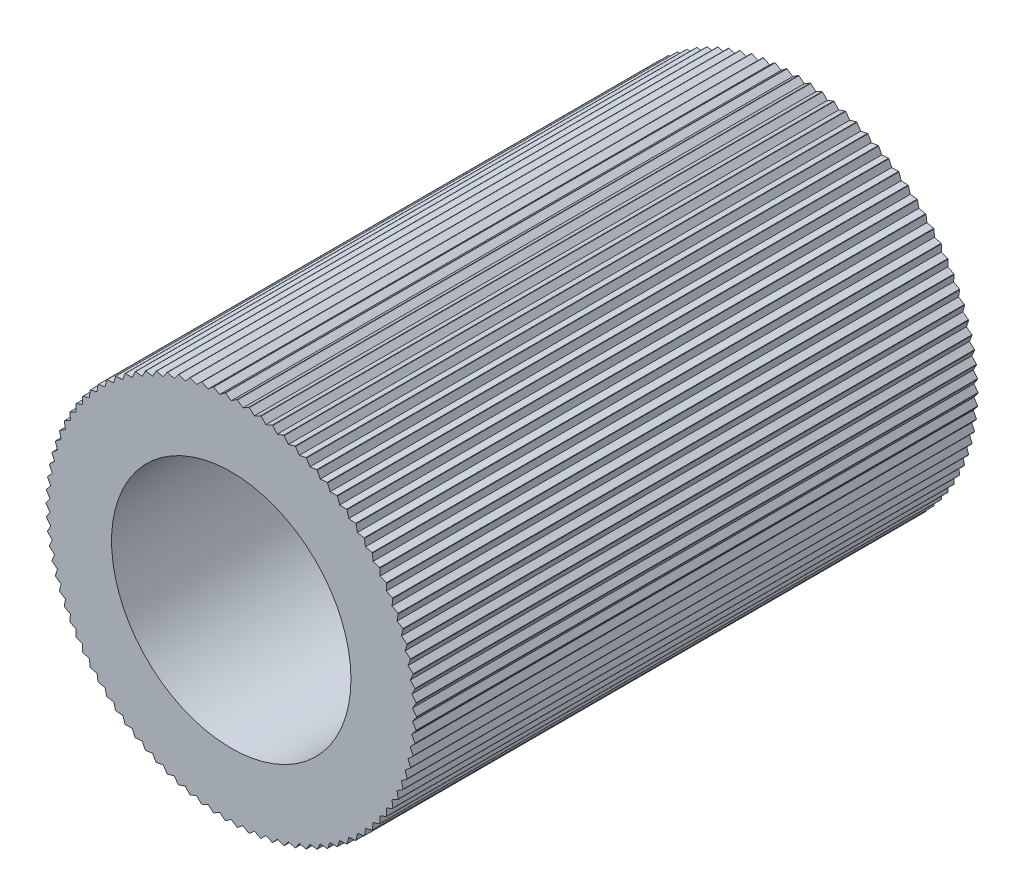
SolidWorks part; units mm, degrees
ref_plane "Alzado" through (0, 0, 0) normal (0, 0, 1) x (1, 0, 0)
ref_plane "Planta" through (0, 0, 0) normal (0, 1, 0) x (1, 0, 0)
ref_plane "Vista lateral" through (0, 0, 0) normal (1, 0, 0) x (0, 0, -1)
sketch "Croquis1" plane through (0, 0, 0) normal (0, 0, 1) x (1, 0, 0)
  circle A0 centre (0, 0) radius 3.25
  dimension "D1" = 6.5
extrude "Saliente-Extruir1" add sketch "Croquis1" along normal blind 9.85
hole_wizard "Perforador para roscar para macho de roscar para M52" positions "Croquis5" profile "Croquis4" hole size "M5" standard "ISO" end condition through all
sketch "Croquis5" plane through (0, 0, 9.85) normal (0, 0, 1) x (1, 0, 0)
  point P0 (0, 0)
sketch "Croquis4" plane through (0, 0, 9.85) normal (1, 0, 0) x (0, -1, 0)
  line L0 (0, 0) -> (0, 9.85)
  line L1 (0, 9.85) -> (2.1, 9.85)
  line L2 (2.1, 9.85) -> (2.1, 0)
  line L5 (2.1, 0) -> (0, 0)
  line L11 (0, -6.35) -> (0, 107.95) construction
  dimension "Diámetro de taladro hasta el siguiente" = 4.2
  dimension "Profundidad de taladro hasta el siguiente" = 9.85
sketch "Croquis6" plane through (0, 0, 9.85) normal (0, 0, 1) x (1, 0, 0)
  line L0 (0, 3.25) -> (0, -3.25) construction
  line L5 (-0.1, 3.2485) -> (0, 3.1808)
  line L6 (0, 3.1808) -> (0.1, 3.2485)
  circle A0 centre (0, 0) radius 3.25 construction
  arc A1 (0.1, 3.2485) -> (-0.1, 3.2485) centre (0, 0) ccw
extrude "Cortar-Extruir1" cut sketch "Croquis6" against normal blind 10
pattern_circular "MatrizC1" count 98 over 360 about axis through (0, 0, 0) along (0, 0, 1) of "Cortar-Extruir1"
